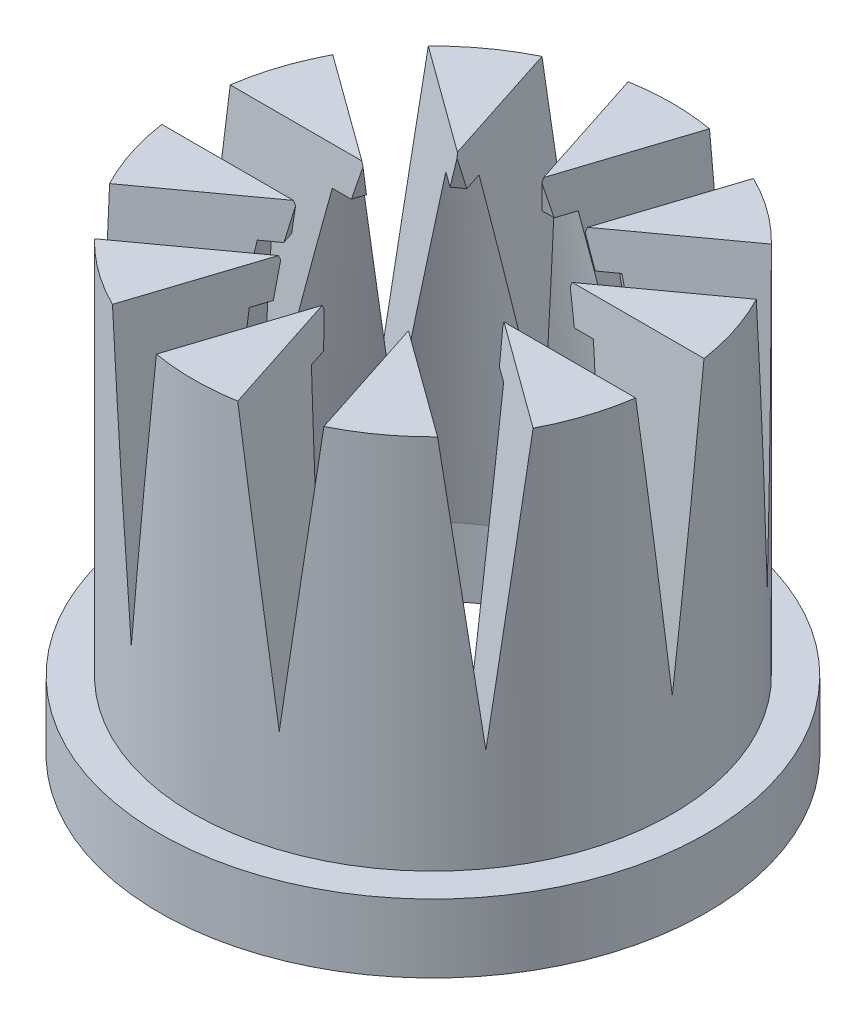
SolidWorks part; units mm, degrees
material "Nickel"
ref_plane "Front Plane" through (0, 0, 0) normal (0, 0, 1) x (1, 0, 0)
ref_plane "Top Plane" through (0, 0, 0) normal (0, 1, 0) x (1, 0, 0)
ref_plane "Right Plane" through (0, 0, 0) normal (1, 0, 0) x (0, 0, -1)
sketch "Sketch1" plane through (0, 0, 0) normal (0, 1, 0) x (1, 0, 0)
  circle A0 centre (0, 0) radius 3.5
  dimension "D1" = 7
extrude "Boss-Extrude1" add sketch "Sketch1" along normal blind 5.5
sketch "Sketch2" plane through (0, 0, 0) normal (0, -1, 0) x (1, 0, 0)
  circle A0 centre (0, 0) radius 2.75
  dimension "D1" = 5.5
extrude "Cut-Extrude1" cut sketch "Sketch2" against normal blind 5.5 draft 12
sketch "Sketch3" plane through (0, 0, 0) normal (1, 0, 0) x (0, 0, -1)
  line L0 (0, 5.5) -> (0, 0) construction
  line L1 (1.5809, 5.5) -> (-1.5809, 5.5) construction
  line L2 (-0.5, 5.5) -> (-0.35, 4.3)
  line L3 (-0.35, 4.3) -> (0, 1.5)
  line L4 (0, 1.5) -> (0.35, 4.3)
  line L5 (0.35, 4.3) -> (0.5, 5.5)
  line L6 (-0.5, 5.5) -> (0.5, 5.5)
  dimension "D1" = 0.5
  dimension "D2" = 0.5
  dimension "D3" = 4
  dimension "D4" = 0.35
  dimension "D5" = 0.35
  dimension "D6" = 1.2
  dimension "D7" = 1.2
extrude "Cut-Extrude2" cut sketch "Sketch3" against normal blind 5.5
pattern_circular "CirPattern1" count 10 over 360 about axis through (0, 5.5, 0) along (0, -1, 0) of "Cut-Extrude2"
sketch "Sketch4" plane through (0, 0, 0) normal (0, -1, 0) x (1, 0, 0)
  circle A0 centre (0, 0) radius 2.75
extrude "Cut-Extrude3" cut sketch "Sketch4" against normal blind 5 draft 9
sketch "Sketch5" plane through (0, 0, 0) normal (0, -1, 0) x (1, 0, 0)
  circle A0 centre (0, 0) radius 2.75
  circle A1 centre (0, 0) radius 2.75
  circle A2 centre (0, 0) radius 4
  circle M1 centre (0, 0) radius 2.75
  circle M2 centre (0, 0) radius 3.5
  dimension "D1" = 8
extrude "Boss-Extrude2" add sketch "Sketch5" along normal blind 1 contours A2 M2 | M2 M1
